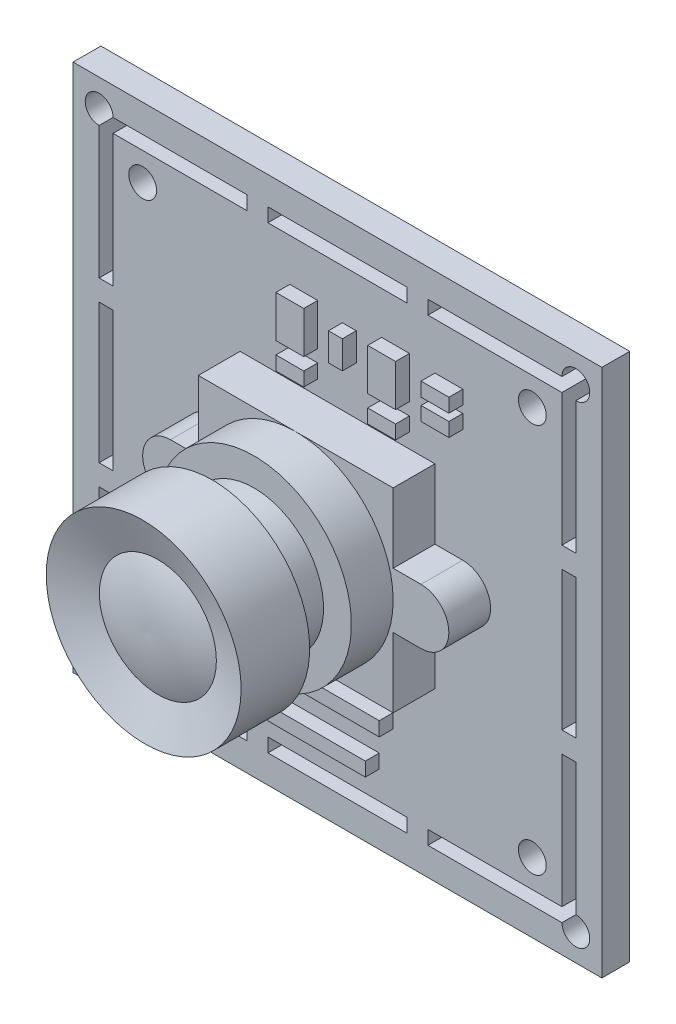
SolidWorks part; units mm, degrees
ref_plane "前视基准面" through (0, 0, 0) normal (0, 0, 1) x (1, 0, 0)
ref_plane "上视基准面" through (0, 0, 0) normal (0, 1, 0) x (1, 0, 0)
ref_plane "右视基准面" through (0, 0, 0) normal (1, 0, 0) x (0, 0, -1)
sketch "草图1" plane through (0, 0, 0) normal (0, 0, 1) x (1, 0, 0)
  line L1 (-19, -19) -> (19, -19)
  line L2 (-19, -19) -> (-19, 19)
  line L3 (-19, 19) -> (19, 19)
  line L4 (19, -19) -> (19, 19)
  line L5 (-19, -19) -> (19, 19) construction
  line L6 (-19, 19) -> (19, -19) construction
  point P0 (0, 0)
  dimension "D1" = 38
  dimension "D2" = 38
extrude "凸台-拉伸1" add sketch "草图1" along normal blind 2
sketch "草图2" plane through (0, 0, 2) normal (0, 0, 1) x (1, 0, 0)
  line L0 (-5, 16.9921) -> (-5, 16)
  line L1 (17.1277, -16.9921) -> (-17.1277, -16.9921)
  line L2 (17.1277, -16.9921) -> (17.1277, 16.9921)
  line L3 (17.1277, 16.9921) -> (-17.1277, 16.9921)
  line L4 (-17.1277, -16.9921) -> (-17.1277, 16.9921)
  line L5 (17.1277, -16.9921) -> (-17.1277, 16.9921) construction
  line L6 (17.1277, 16.9921) -> (-17.1277, -16.9921) construction
  line L7 (16.1277, -16) -> (-16.1277, -16)
  line L8 (16.1277, -16) -> (16.1277, 16)
  line L9 (16.1277, 16) -> (-16.1277, 16)
  line L10 (-16.1277, -16) -> (-16.1277, 16)
  line L11 (16.1277, -16) -> (-16.1277, 16) construction
  line L12 (16.1277, 16) -> (-16.1277, -16) construction
  line L13 (5, 16.9921) -> (5, 16)
  line L14 (0, -1.1) -> (0, 1.1) construction
  line L15 (-6.5, 16.9921) -> (-6.5, 16)
  line L16 (6.5, 16.9921) -> (6.5, 16)
  line L17 (5, -16) -> (5, -16.9921)
  line L18 (-5, -16) -> (-5, -16.9921)
  line L19 (17.1277, -5) -> (16.1277, -5)
  line L20 (16.1277, 5) -> (17.1277, 5)
  line L21 (-16.1277, 5) -> (-17.1277, 5)
  line L22 (-16.1277, -5) -> (-17.1277, -5)
  line L23 (-6.5, -16) -> (-6.5, -16.9921)
  line L24 (6.5, -16) -> (6.5, -16.9921)
  line L25 (1.1, 0) -> (-1.1, 0) construction
  line L26 (17.1277, -6.5) -> (16.1277, -6.5)
  line L27 (17.1277, 6.5) -> (16.1277, 6.5)
  line L29 (-16.1277, 6.5) -> (-17.1277, 6.5)
  line L30 (-17.1277, -6.5) -> (-16.1277, -6.5)
  line L31 (-14, -14) -> (14, -14) construction
  line L32 (-14, -14) -> (-14, 14) construction
  line L33 (-14, 14) -> (14, 14) construction
  line L34 (14, -14) -> (14, 14) construction
  line L35 (-14, -14) -> (14, 14) construction
  line L36 (-14, 14) -> (14, -14) construction
  circle A0 centre (-17.1277, 16.9921) radius 1
  circle A1 centre (17.1277, 16.9921) radius 1
  circle A2 centre (-17.1277, -16.9921) radius 1
  circle A3 centre (17.1277, -16.9921) radius 1
  circle A4 centre (-14, 14) radius 1
  circle A5 centre (14, 14) radius 1
  circle A6 centre (-14, -14) radius 1
  circle A7 centre (14, -14) radius 1
  point P0 (0, 0)
  point P6 (0, 0)
  point P51 (-16.6277, 5)
  point P52 (0, 0)
  dimension "D4" = 2
  dimension "D23" = 2
  dimension "D1" = 32
  dimension "D2" = 1
  dimension "D3" = 32.2555
  dimension "D5" = 10
  dimension "D6" = 5
  dimension "D7" = 1.5
  dimension "D8" = 1.5
  dimension "D9" = 10
  dimension "D10" = 5
  dimension "D11" = 1.5
  dimension "D12" = 1.5
  dimension "D13" = 10
  dimension "D14" = 5
  dimension "D15" = 10
  dimension "D16" = 5
  dimension "D17" = 1.5
  dimension "D18" = 1.5
  dimension "D19" = 1.5
  dimension "D20" = 1.5
  dimension "D21" = 28
  dimension "D22" = 28
extrude "切除-拉伸1" cut sketch "草图2" against normal blind 2 contours A0 L4 L29 L10 L9 L15 L3 | L13 L3 L0 L9 | A1 L3 L16 L9 L8 L27 L2 | L22 L10 L21 L4 | L20 L8 L19 L2 | A2 L1 L23 L7 L10 L30 L4 | L7 L18 L1 L17 | A3 L2 L26 L8 L7 L24 L1 | A4 | A6 | A7 | A5
sketch "草图3" plane through (0, 0, 2) normal (0, 0, 1) x (1, 0, 0)
  line L0 (-9, 0) -> (9, 0) construction
  line L1 (-7, -7) -> (7, -7)
  line L2 (-7, -7) -> (-7, 7)
  line L3 (-7, 7) -> (7, 7)
  line L4 (7, -7) -> (7, 7)
  line L5 (-7, -7) -> (7, 7) construction
  line L6 (-7, 7) -> (7, -7) construction
  line L7 (1.1, 0) -> (-1.1, 0) construction
  line L8 (-9, 2) -> (9, 2)
  line L9 (-9, -2) -> (9, -2)
  line L10 (0, -1.1) -> (0, 1.1) construction
  arc A0 (-9, 2) -> (-9, -2) centre (-9, 0) ccw
  arc A1 (9, -2) -> (9, 2) centre (9, 0) ccw
  point P0 (0, 0)
  point P10 (0, 0)
  dimension "D5" = 2
  dimension "D1" = 14
  dimension "D2" = 14
  dimension "D3" = 18
  dimension "D4" = 9
extrude "凸台-拉伸2" add sketch "草图3" along normal blind 3 contours L8 A0 L9 L2 | L9 A1 L8 L4
sketch "草图4" plane through (0, 0, 0) normal (1, 0, 0) x (0, 0, -1)
  line L0 (-5, 0) -> (-16, 0)
  line L1 (-5, 2) -> (-5, -2) construction
  line L2 (2.75, 0) -> (-2.75, 0) construction
  line L3 (-16, 0) -> (-16, 7)
  line L4 (-16, 7) -> (-11, 7)
  line L5 (-11, 7) -> (-11, 5)
  line L6 (-11, 5) -> (-8, 5)
  line L7 (-8, 5) -> (-8, 7)
  line L8 (-8, 7) -> (-5, 7)
  line L9 (-5, 2) -> (-5, 7) construction
  line L10 (-5, 7) -> (-5, 0)
  dimension "D1" = 7
  dimension "D2" = 7
  dimension "D3" = 2
  dimension "D4" = 11
  dimension "D5" = 5
  dimension "D6" = 3
revolve "旋转1" add sketch "草图4" angle 360 about L0
sketch "草图5" plane through (0, 0, 0) normal (1, 0, 0) x (0, 0, -1)
  line L0 (-16, 7) -> (-14.9081, 4)
  line L2 (-16, 7) -> (-16, -0.2044)
  line L4 (-16, -0.2044) -> (-15.6574, -0.2044)
  arc A0 (-14.9081, 4) -> (-15.6574, -0.2044) centre (-5.6649, 0.1838) ccw
  dimension "D1" = 20
  dimension "D5" = 10
  dimension "D3" = 3
revolve "切除-旋转2" cut sketch "草图5" angle 360 about L4
sketch "草图6" plane through (0, 0, 2) normal (0, 0, 1) x (1, 0, 0)
  line L1 (-14, -6) -> (-11, -6)
  line L2 (-14, -6) -> (-14, -11)
  line L3 (-14, -11) -> (-11, -11)
  line L4 (-11, -6) -> (-11, -11)
  line L5 (-14, -6) -> (-11, -11) construction
  line L6 (-14, -11) -> (-11, -6) construction
  line L7 (-12, -15) -> (-7, -15)
  line L8 (-12, -15) -> (-12, -12)
  line L9 (-12, -12) -> (-7, -12)
  line L10 (-7, -15) -> (-7, -12)
  line L11 (-12, -15) -> (-7, -12) construction
  line L12 (-12, -12) -> (-7, -15) construction
  line L13 (-3.4243, 9.9539) -> (-1.4243, 9.9539)
  line L14 (-3.4243, 9.9539) -> (-3.4243, 12.9539)
  line L15 (-3.4243, 12.9539) -> (-1.4243, 12.9539)
  line L16 (-1.4243, 9.9539) -> (-1.4243, 12.9539)
  line L17 (-3.4243, 9.9539) -> (-1.4243, 12.9539) construction
  line L18 (-3.4243, 12.9539) -> (-1.4243, 9.9539) construction
  line L19 (0.3489, 10.4539) -> (1.3489, 10.4539)
  line L20 (0.3489, 10.4539) -> (0.3489, 12.4539)
  line L21 (0.3489, 12.4539) -> (1.3489, 12.4539)
  line L22 (1.3489, 10.4539) -> (1.3489, 12.4539)
  line L23 (0.3489, 10.4539) -> (1.3489, 12.4539) construction
  line L24 (0.3489, 12.4539) -> (1.3489, 10.4539) construction
  line L25 (3.1716, 9.9539) -> (5.1716, 9.9539)
  line L26 (3.1716, 9.9539) -> (3.1716, 12.9539)
  line L27 (3.1716, 12.9539) -> (5.1716, 12.9539)
  line L28 (5.1716, 9.9539) -> (5.1716, 12.9539)
  line L29 (3.1716, 9.9539) -> (5.1716, 12.9539) construction
  line L30 (3.1716, 12.9539) -> (5.1716, 9.9539) construction
  line L31 (7.0041, 12.6483) -> (9.0041, 12.6483)
  line L32 (7.0041, 12.6483) -> (7.0041, 11.6483)
  line L33 (7.0041, 11.6483) -> (9.0041, 11.6483)
  line L34 (9.0041, 12.6483) -> (9.0041, 11.6483)
  line L35 (7.0041, 12.6483) -> (9.0041, 11.6483) construction
  line L36 (7.0041, 11.6483) -> (9.0041, 12.6483) construction
  line L37 (7.0041, 11.135) -> (9.0041, 11.135)
  line L38 (7.0041, 11.135) -> (7.0041, 10.135)
  line L39 (7.0041, 10.135) -> (9.0041, 10.135)
  line L40 (9.0041, 11.135) -> (9.0041, 10.135)
  line L41 (7.0041, 11.135) -> (9.0041, 10.135) construction
  line L42 (7.0041, 10.135) -> (9.0041, 11.135) construction
  line L43 (-3.4243, 9.0633) -> (-1.4243, 9.0633)
  line L44 (-3.4243, 9.0633) -> (-3.4243, 8.0633)
  line L45 (-3.4243, 8.0633) -> (-1.4243, 8.0633)
  line L46 (-1.4243, 9.0633) -> (-1.4243, 8.0633)
  line L47 (-3.4243, 9.0633) -> (-1.4243, 8.0633) construction
  line L48 (-3.4243, 8.0633) -> (-1.4243, 9.0633) construction
  line L49 (3.1716, 9.0633) -> (5.1716, 9.0633)
  line L50 (3.1716, 9.0633) -> (3.1716, 8.0633)
  line L51 (3.1716, 8.0633) -> (5.1716, 8.0633)
  line L52 (5.1716, 9.0633) -> (5.1716, 8.0633)
  line L53 (3.1716, 9.0633) -> (5.1716, 8.0633) construction
  line L54 (3.1716, 8.0633) -> (5.1716, 9.0633) construction
  line L55 (-10, -10.5) -> (-9.5, -10.5)
  line L56 (-10, -10.5) -> (-10, -8.5)
  line L57 (-10, -8.5) -> (-9.5, -8.5)
  line L58 (-9.5, -10.5) -> (-9.5, -8.5)
  line L59 (-10, -10.5) -> (-9.5, -8.5) construction
  line L60 (-10, -8.5) -> (-9.5, -10.5) construction
  line L61 (-8.5, -10.5) -> (-8, -10.5)
  line L62 (-8.5, -10.5) -> (-8.5, -8.5)
  line L63 (-8.5, -8.5) -> (-8, -8.5)
  line L64 (-8, -10.5) -> (-8, -8.5)
  line L65 (-8.5, -10.5) -> (-8, -8.5) construction
  line L66 (-8.5, -8.5) -> (-8, -10.5) construction
  line L67 (-5, -9.9862) -> (4, -9.9862)
  line L68 (-5, -9.9862) -> (-5, -11)
  line L69 (-5, -11) -> (4, -11)
  line L70 (4, -9.9862) -> (4, -11)
  line L71 (-5, -9.9862) -> (4, -11) construction
  line L72 (-5, -11) -> (4, -9.9862) construction
  line L73 (-4, -13) -> (3, -13)
  line L74 (-4, -13) -> (-4, -14)
  line L75 (-4, -14) -> (3, -14)
  line L76 (3, -13) -> (3, -14)
  line L77 (-4, -13) -> (3, -14) construction
  line L78 (-4, -14) -> (3, -13) construction
  line L79 (-19, -19) -> (19, -19) construction
  line L80 (-19, 19) -> (-19, -19) construction
  line L81 (0, -8.8) -> (0, 8.8) construction
  point P0 (-12.5, -8.5)
  point P5 (-9.5, -13.5)
  point P10 (-2.4243, 11.4539)
  point P15 (0.8489, 11.4539)
  point P20 (4.1716, 11.4539)
  point P25 (8.0041, 12.1483)
  point P30 (8.0041, 10.635)
  point P35 (-2.4243, 8.5633)
  point P40 (4.1716, 8.5633)
  point P45 (-9.75, -9.5)
  point P50 (-8.25, -9.5)
  point P55 (-0.5, -10.4931)
  point P60 (-0.5, -13.5)
  dimension "D1" = 3
  dimension "D2" = 5
  dimension "D3" = 5
  dimension "D4" = 3
  dimension "D5" = 8
  dimension "D6" = 5
  dimension "D7" = 7
  dimension "D8" = 4
  dimension "D9" = 0.5
  dimension "D10" = 0.5
  dimension "D11" = 2
  dimension "D12" = 2
  dimension "D13" = 1
  dimension "D14" = 1
  dimension "D15" = 0.5
  dimension "D16" = 0.5
  dimension "D17" = 7
  dimension "D18" = 1
  dimension "D19" = 0.5
  dimension "D20" = 1
  dimension "D21" = 9
  dimension "D22" = 0.5
  dimension "D23" = 2
  dimension "D24" = 2
  dimension "D25" = 3
  dimension "D26" = 2
  dimension "D27" = 3
  dimension "D28" = 1
  dimension "D29" = 2
  dimension "D30" = 2
  dimension "D31" = 1
  dimension "D32" = 2
  dimension "D33" = 1
  dimension "D34" = 2
  dimension "D35" = 1
  dimension "D36" = 2
  dimension "D37" = 1
extrude "凸台-拉伸3" add sketch "草图6" along normal blind 1
sketch "草图7" plane through (0, 0, 0) normal (0, 0, -1) x (-1, 0, 0)
  line L0 (0, 8.8) -> (0, -8.8) construction
  line L1 (-4.75, -16) -> (4.75, -16)
  line L2 (-4.75, -16) -> (-4.75, -11)
  line L3 (-4.75, -11) -> (4.75, -11)
  line L4 (4.75, -16) -> (4.75, -11)
  line L5 (-4.75, -16) -> (4.75, -11) construction
  line L6 (-4.75, -11) -> (4.75, -16) construction
  line L7 (-16.1277, -16) -> (-6.5, -16) construction
  line L8 (-4.75, -12.7) -> (-2.85, -12.7) construction
  line L9 (-2.85, -12.7) -> (-0.95, -12.7) construction
  line L10 (-0.95, -12.7) -> (0.95, -12.7) construction
  line L11 (0.95, -12.7) -> (2.85, -12.7) construction
  line L12 (2.85, -12.7) -> (4.75, -12.7) construction
  line L17 (-4.45, -15.7) -> (-4.45, -11.3)
  line L18 (-4.45, -11.3) -> (4.45, -11.3)
  line L19 (4.45, -15.7) -> (4.45, -11.3)
  line L20 (-4.45, -15.7) -> (4.45, -15.7)
  line L21 (-9, 9) -> (-9, -9)
  line L22 (-9, -9) -> (9, -9)
  line L23 (9, -9) -> (9, 9)
  line L24 (9, 9) -> (-9, 9)
  line L25 (-9, 9) -> (-9, -9)
  line L26 (-9, -9) -> (9, -9)
  line L27 (9, -9) -> (9, 9)
  line L28 (9, 9) -> (-9, 9)
  circle A0 centre (-2.85, -12.7) radius 0.125
  circle A1 centre (-0.95, -12.7) radius 0.125
  circle A2 centre (0.95, -12.7) radius 0.125
  circle A3 centre (2.85, -12.7) radius 0.125
  point P0 (0, -13.5)
  dimension "D5" = 0.25
  dimension "D1" = 5
  dimension "D2" = 9.5
  dimension "D3" = 2.5
  dimension "D4" = 1.9
  dimension "D6" = 0.8
  dimension "D7" = 10
  dimension "D8" = 0.3
extrude "6" add sketch "草图7" along normal blind 6 contours L1 L4 L3 L2 L20 L17 L18 L19 | A2 | A3 | A0 | A1
sketch "草图8" plane through (0, 0, 0) normal (0, 0, -1) x (-1, 0, 0)
  line L0 (12.1, 0) -> (-12.1, 0) construction
  line L1 (4.2248, -2.6022) -> (9.919, -2.6022)
  line L2 (4.2248, -2.6022) -> (4.2248, -7.9903)
  line L3 (4.2248, -7.9903) -> (9.919, -7.9903)
  line L4 (9.919, -2.6022) -> (9.919, -7.9903)
  line L5 (7.776, 10.1945) -> (12.3681, 10.1945)
  line L6 (7.776, 10.1945) -> (7.776, 6.3371)
  line L7 (7.776, 6.3371) -> (12.3681, 6.3371)
  line L8 (12.3681, 10.1945) -> (12.3681, 6.3371)
  line L9 (12.3681, -2.0512) -> (13.5315, -2.0512)
  line L10 (12.3681, -2.0512) -> (12.3681, -2.6022)
  line L11 (12.3681, -2.6022) -> (13.5315, -2.6022)
  line L12 (13.5315, -2.0512) -> (13.5315, -2.6022)
  line L13 (12.3681, -3.4594) -> (13.5315, -3.4594)
  line L14 (12.3681, -3.4594) -> (12.3681, -3.9492)
  line L15 (12.3681, -3.9492) -> (13.5315, -3.9492)
  line L16 (13.5315, -3.4594) -> (13.5315, -3.9492)
  line L17 (12.3681, -4.7452) -> (13.5315, -4.7452)
  line L18 (12.3681, -4.7452) -> (12.3681, -5.2963)
  line L19 (12.3681, -5.2963) -> (13.5315, -5.2963)
  line L20 (13.5315, -4.7452) -> (13.5315, -5.2963)
  line L21 (12.9498, -6.1535) -> (13.5315, -6.1535)
  line L22 (12.9498, -6.1535) -> (12.9498, -6.7657)
  line L23 (12.9498, -6.7657) -> (13.5315, -6.7657)
  line L24 (13.5315, -6.1535) -> (13.5315, -6.7657)
  line L25 (10.715, -9.7659) -> (12.3681, -9.7659)
  line L26 (10.715, -9.7659) -> (10.715, -12.2151)
  line L27 (10.715, -12.2151) -> (12.3681, -12.2151)
  line L28 (12.3681, -9.7659) -> (12.3681, -12.2151)
  line L29 (13.5315, -9.3986) -> (14.756, -9.3986)
  line L30 (13.5315, -9.3986) -> (13.5315, -11.5415)
  line L31 (13.5315, -11.5415) -> (14.756, -11.5415)
  line L32 (14.756, -9.3986) -> (14.756, -11.5415)
  line L33 (-9.3067, -9.3986) -> (-7.2862, -9.3986)
  line L34 (-9.3067, -9.3986) -> (-9.3067, -11.5415)
  line L35 (-9.3067, -11.5415) -> (-7.2862, -11.5415)
  line L36 (-7.2862, -9.3986) -> (-7.2862, -11.5415)
  line L37 (-10.1639, -6.4596) -> (-7.2862, -6.4596)
  line L38 (-10.1639, -6.4596) -> (-10.1639, -7.4392)
  line L39 (-10.1639, -7.4392) -> (-7.2862, -7.4392)
  line L40 (-7.2862, -6.4596) -> (-7.2862, -7.4392)
  line L41 (-5.0207, -7.9903) -> (-3.1839, -7.9903)
  line L42 (-5.0207, -7.9903) -> (-5.0207, -8.9087)
  line L43 (-5.0207, -8.9087) -> (-3.1839, -8.9087)
  line L44 (-3.1839, -7.9903) -> (-3.1839, -8.9087)
  line L45 (-5.3881, -1.3776) -> (-3.5512, -1.3776)
  line L46 (-5.3881, -1.3776) -> (-5.3881, -2.6022)
  line L47 (-5.3881, -2.6022) -> (-3.5512, -2.6022)
  line L48 (-3.5512, -1.3776) -> (-3.5512, -2.6022)
  line L49 (-5.3881, -3.7043) -> (-3.5512, -3.7043)
  line L50 (-5.3881, -3.7043) -> (-5.3881, -3.9492)
  line L51 (-5.3881, -3.9492) -> (-3.5512, -3.9492)
  line L52 (-3.5512, -3.7043) -> (-3.5512, -3.9492)
  line L54 (-10.7762, 13.1335) -> (-10.1639, 13.1335)
  line L55 (-10.7762, 13.1335) -> (-10.7762, 10.8068)
  line L56 (-10.7762, 10.8068) -> (-10.1639, 10.8068)
  line L57 (-10.1639, 13.1335) -> (-10.1639, 10.8068)
  line L58 (-8.6332, 12.7661) -> (-7.2862, 12.7661)
  line L59 (-8.6332, 12.7661) -> (-8.6332, 12.3375)
  line L60 (-8.6332, 12.3375) -> (-7.2862, 12.3375)
  line L61 (-7.2862, 12.7661) -> (-7.2862, 12.3375)
  line L62 (-8.6332, 11.9701) -> (-7.2862, 11.9701)
  line L63 (-8.6332, 11.9701) -> (-8.6332, 11.2354)
  line L64 (-8.6332, 11.2354) -> (-7.2862, 11.2354)
  line L65 (-7.2862, 11.9701) -> (-7.2862, 11.2354)
  line L66 (-5.8779, 13.1335) -> (-5.3881, 13.1335)
  line L67 (-5.8779, 13.1335) -> (-5.8779, 11.2354)
  line L68 (-5.8779, 11.2354) -> (-5.3881, 11.2354)
  line L69 (-5.3881, 13.1335) -> (-5.3881, 11.2354)
  line L70 (-4.1023, 12.5518) -> (-3.1839, 12.5518)
  line L71 (-4.1023, 12.5518) -> (-4.1023, 12.1844)
  line L72 (-4.1023, 12.1844) -> (-3.1839, 12.1844)
  line L73 (-3.1839, 12.5518) -> (-3.1839, 12.1844)
  line L74 (-4.1023, 11.6028) -> (-3.1839, 11.6028)
  line L75 (-4.1023, 11.6028) -> (-4.1023, 11.2354)
  line L76 (-4.1023, 11.2354) -> (-3.1839, 11.2354)
  line L77 (-3.1839, 11.6028) -> (-3.1839, 11.2354)
  circle A0 centre (-9.3067, 0) radius 1.5911
  circle A1 centre (7.3474, 0) radius 1.5383
extrude "凸台-拉伸5" add sketch "草图8" along normal blind 1
